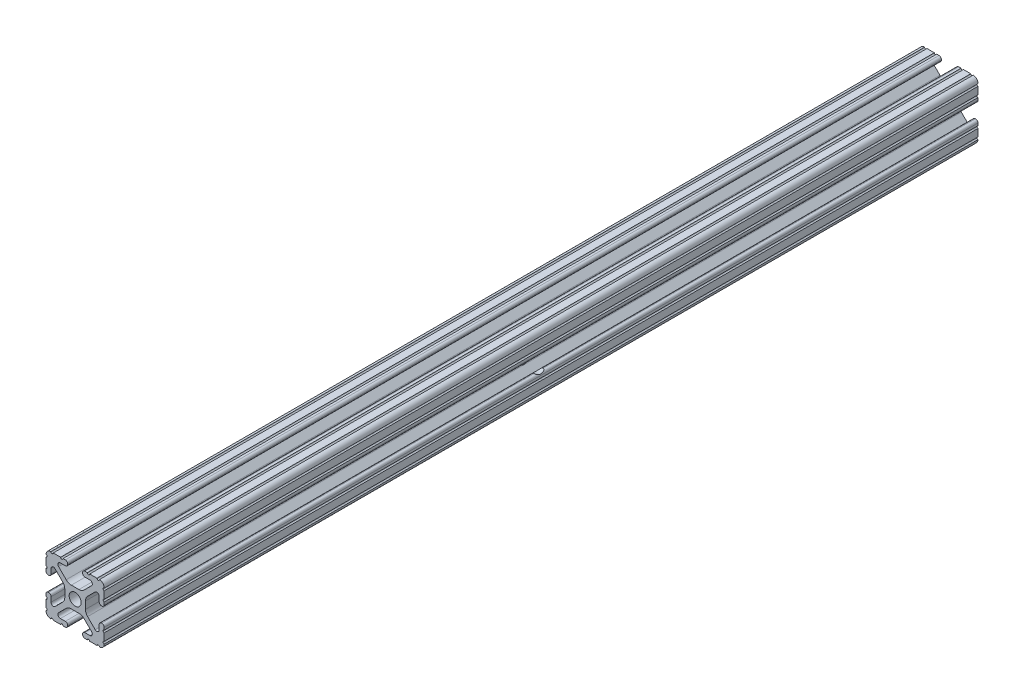
SolidWorks part; units mm, degrees
ref_plane "Front Plane" through (0, 0, 0) normal (0, 0, 1) x (1, 0, 0)
ref_plane "Top Plane" through (0, 0, 0) normal (0, 1, 0) x (1, 0, 0)
ref_plane "Right Plane" through (0, 0, 0) normal (1, 0, 0) x (0, 0, -1)
sketch "Sketch1" plane through (0, 0, 0) normal (0, 0, 1) x (1, 0, 0)
  line L88 (-7.1797, -8.6452) -> (-3.9523, -5.4237)
  line L89 (-1.7093, -4.4958) -> (1.7093, -4.4958)
  line L90 (3.9523, -5.4237) -> (7.1797, -8.6452)
  line L91 (6.4164, -10.4902) -> (4.2875, -10.4902)
  line L92 (3.2385, -11.5392) -> (3.2385, -11.651)
  line L93 (4.2875, -12.7) -> (5.3171, -12.7)
  line L94 (6.3331, -12.7) -> (9.5504, -12.7)
  line L95 (12.7, -9.5504) -> (12.7, -6.3331)
  line L96 (12.7, -5.3171) -> (12.7, -4.2875)
  line L97 (11.651, -3.2385) -> (11.5392, -3.2385)
  line L98 (10.4902, -4.2875) -> (10.4902, -6.4021)
  line L99 (8.7371, -7.1294) -> (5.441, -3.8408)
  line L100 (4.5085, -1.5932) -> (4.5085, 1.5932)
  line L101 (5.441, 3.8408) -> (8.7371, 7.1294)
  line L102 (10.4902, 6.4021) -> (10.4902, 4.2875)
  line L103 (11.5392, 3.2385) -> (11.651, 3.2385)
  line L104 (12.7, 4.2875) -> (12.7, 5.3171)
  line L105 (12.7, 6.3331) -> (12.7, 9.5504)
  line L106 (9.5504, 12.7) -> (6.3331, 12.7)
  line L107 (5.3171, 12.7) -> (4.2875, 12.7)
  line L108 (3.2385, 11.651) -> (3.2385, 11.5392)
  line L109 (4.2875, 10.4902) -> (6.4768, 10.4902)
  line L110 (7.207, 8.7244) -> (3.8983, 5.4232)
  line L111 (1.6558, 4.4958) -> (-1.6558, 4.4958)
  line L112 (-3.8983, 5.4232) -> (-7.207, 8.7244)
  line L113 (-6.4768, 10.4902) -> (-4.2875, 10.4902)
  line L114 (-3.2385, 11.5392) -> (-3.2385, 11.651)
  line L115 (-4.2875, 12.7) -> (-5.3171, 12.7)
  line L116 (-6.3331, 12.7) -> (-9.5504, 12.7)
  line L117 (-12.7, 9.5504) -> (-12.7, 6.3331)
  line L118 (-12.7, 5.3171) -> (-12.7, 4.2875)
  line L119 (-11.651, 3.2385) -> (-11.5392, 3.2385)
  line L120 (-10.4902, 4.2875) -> (-10.4902, 6.4021)
  line L121 (-8.7371, 7.1294) -> (-5.441, 3.8408)
  line L122 (-4.5085, 1.5932) -> (-4.5085, -1.5932)
  line L123 (-5.441, -3.8408) -> (-8.7371, -7.1294)
  line L124 (-10.4902, -6.4021) -> (-10.4902, -4.2875)
  line L125 (-11.5392, -3.2385) -> (-11.651, -3.2385)
  line L126 (-12.7, -4.2875) -> (-12.7, -5.3171)
  line L127 (-12.7, -6.3331) -> (-12.7, -9.5504)
  line L128 (-9.5504, -12.7) -> (-6.3331, -12.7)
  line L129 (-5.3171, -12.7) -> (-4.2875, -12.7)
  line L130 (-3.2385, -11.651) -> (-3.2385, -11.5392)
  line L131 (-4.2875, -10.4902) -> (-6.4164, -10.4902)
  circle A1 centre (0, 0) radius 2.6035
  arc A104 (-7.1797, -8.6452) -> (-6.4164, -10.4902) centre (-6.4164, -9.4098) ccw
  arc A105 (-1.7093, -4.4958) -> (-3.9523, -5.4237) centre (-1.7093, -7.6708) ccw
  arc A106 (3.9523, -5.4237) -> (1.7093, -4.4958) centre (1.7093, -7.6708) ccw
  arc A107 (6.4164, -10.4902) -> (7.1797, -8.6452) centre (6.4164, -9.4098) ccw
  arc A108 (4.2875, -10.4902) -> (3.2385, -11.5392) centre (4.2875, -11.5392) ccw
  arc A109 (3.2385, -11.651) -> (4.2875, -12.7) centre (4.2875, -11.651) ccw
  arc A110 (6.3331, -12.7) -> (5.3171, -12.7) centre (5.8251, -12.7) ccw
  arc A111 (10.5664, -12.6998) -> (9.5504, -12.7) centre (10.0584, -12.7) ccw
  arc A112 (10.5664, -12.6998) -> (12.6998, -10.5664) centre (10.5918, -10.5918) ccw
  arc A113 (12.7, -9.5504) -> (12.6998, -10.5664) centre (12.7, -10.0584) ccw
  arc A114 (12.7, -5.3171) -> (12.7, -6.3331) centre (12.7, -5.8251) ccw
  arc A115 (12.7, -4.2875) -> (11.651, -3.2385) centre (11.651, -4.2875) ccw
  arc A116 (11.5392, -3.2385) -> (10.4902, -4.2875) centre (11.5392, -4.2875) ccw
  arc A117 (8.7371, -7.1294) -> (10.4902, -6.4021) centre (9.4628, -6.4021) ccw
  arc A118 (4.5085, -1.5932) -> (5.441, -3.8408) centre (7.6835, -1.5932) ccw
  arc A119 (5.441, 3.8408) -> (4.5085, 1.5932) centre (7.6835, 1.5932) ccw
  arc A120 (10.4902, 6.4021) -> (8.7371, 7.1294) centre (9.4628, 6.4021) ccw
  arc A121 (10.4902, 4.2875) -> (11.5392, 3.2385) centre (11.5392, 4.2875) ccw
  arc A122 (11.651, 3.2385) -> (12.7, 4.2875) centre (11.651, 4.2875) ccw
  arc A123 (12.7, 6.3331) -> (12.7, 5.3171) centre (12.7, 5.8251) ccw
  arc A124 (12.6998, 10.5664) -> (12.7, 9.5504) centre (12.7, 10.0584) ccw
  arc A125 (12.6998, 10.5664) -> (10.5664, 12.6998) centre (10.5918, 10.5918) ccw
  arc A126 (9.5504, 12.7) -> (10.5664, 12.6998) centre (10.0584, 12.7) ccw
  arc A127 (5.3171, 12.7) -> (6.3331, 12.7) centre (5.8251, 12.7) ccw
  arc A128 (4.2875, 12.7) -> (3.2385, 11.651) centre (4.2875, 11.651) ccw
  arc A129 (3.2385, 11.5392) -> (4.2875, 10.4902) centre (4.2875, 11.5392) ccw
  arc A130 (7.207, 8.7244) -> (6.4768, 10.4902) centre (6.4768, 9.4563) ccw
  arc A131 (1.6558, 4.4958) -> (3.8983, 5.4232) centre (1.6558, 7.6708) ccw
  arc A132 (-3.8983, 5.4232) -> (-1.6558, 4.4958) centre (-1.6558, 7.6708) ccw
  arc A133 (-6.4768, 10.4902) -> (-7.207, 8.7244) centre (-6.4768, 9.4563) ccw
  arc A134 (-4.2875, 10.4902) -> (-3.2385, 11.5392) centre (-4.2875, 11.5392) ccw
  arc A135 (-3.2385, 11.651) -> (-4.2875, 12.7) centre (-4.2875, 11.651) ccw
  arc A136 (-6.3331, 12.7) -> (-5.3171, 12.7) centre (-5.8251, 12.7) ccw
  arc A137 (-10.5664, 12.6998) -> (-9.5504, 12.7) centre (-10.0584, 12.7) ccw
  arc A138 (-10.5664, 12.6998) -> (-12.6998, 10.5664) centre (-10.5918, 10.5918) ccw
  arc A139 (-12.7, 9.5504) -> (-12.6998, 10.5664) centre (-12.7, 10.0584) ccw
  arc A140 (-12.7, 5.3171) -> (-12.7, 6.3331) centre (-12.7, 5.8251) ccw
  arc A141 (-12.7, 4.2875) -> (-11.651, 3.2385) centre (-11.651, 4.2875) ccw
  arc A142 (-11.5392, 3.2385) -> (-10.4902, 4.2875) centre (-11.5392, 4.2875) ccw
  arc A143 (-8.7371, 7.1294) -> (-10.4902, 6.4021) centre (-9.4628, 6.4021) ccw
  arc A144 (-4.5085, 1.5932) -> (-5.441, 3.8408) centre (-7.6835, 1.5932) ccw
  arc A145 (-5.441, -3.8408) -> (-4.5085, -1.5932) centre (-7.6835, -1.5932) ccw
  arc A146 (-10.4902, -6.4021) -> (-8.7371, -7.1294) centre (-9.4628, -6.4021) ccw
  arc A147 (-10.4902, -4.2875) -> (-11.5392, -3.2385) centre (-11.5392, -4.2875) ccw
  arc A148 (-11.651, -3.2385) -> (-12.7, -4.2875) centre (-11.651, -4.2875) ccw
  arc A149 (-12.7, -6.3331) -> (-12.7, -5.3171) centre (-12.7, -5.8251) ccw
  arc A150 (-12.6998, -10.5664) -> (-12.7, -9.5504) centre (-12.7, -10.0584) ccw
  arc A151 (-12.6998, -10.5664) -> (-10.5664, -12.6998) centre (-10.5918, -10.5918) ccw
  arc A152 (-9.5504, -12.7) -> (-10.5664, -12.6998) centre (-10.0584, -12.7) ccw
  arc A153 (-5.3171, -12.7) -> (-6.3331, -12.7) centre (-5.8251, -12.7) ccw
  arc A154 (-4.2875, -12.7) -> (-3.2385, -11.651) centre (-4.2875, -11.651) ccw
  arc A155 (-3.2385, -11.5392) -> (-4.2875, -10.4902) centre (-4.2875, -11.5392) ccw
extrude "Boss-Extrude1" add sketch "Sketch1" along normal mid plane 381
sketch "Sketch2" plane through (-12.7, 0, 0) normal (-1, 0, 0) x (0, 0, 1)
  circle A0 centre (0, 0) radius 3.81
  dimension "D1" = 7.62
extrude "Cut-Extrude1" cut sketch "Sketch2" against normal blind 25.4
